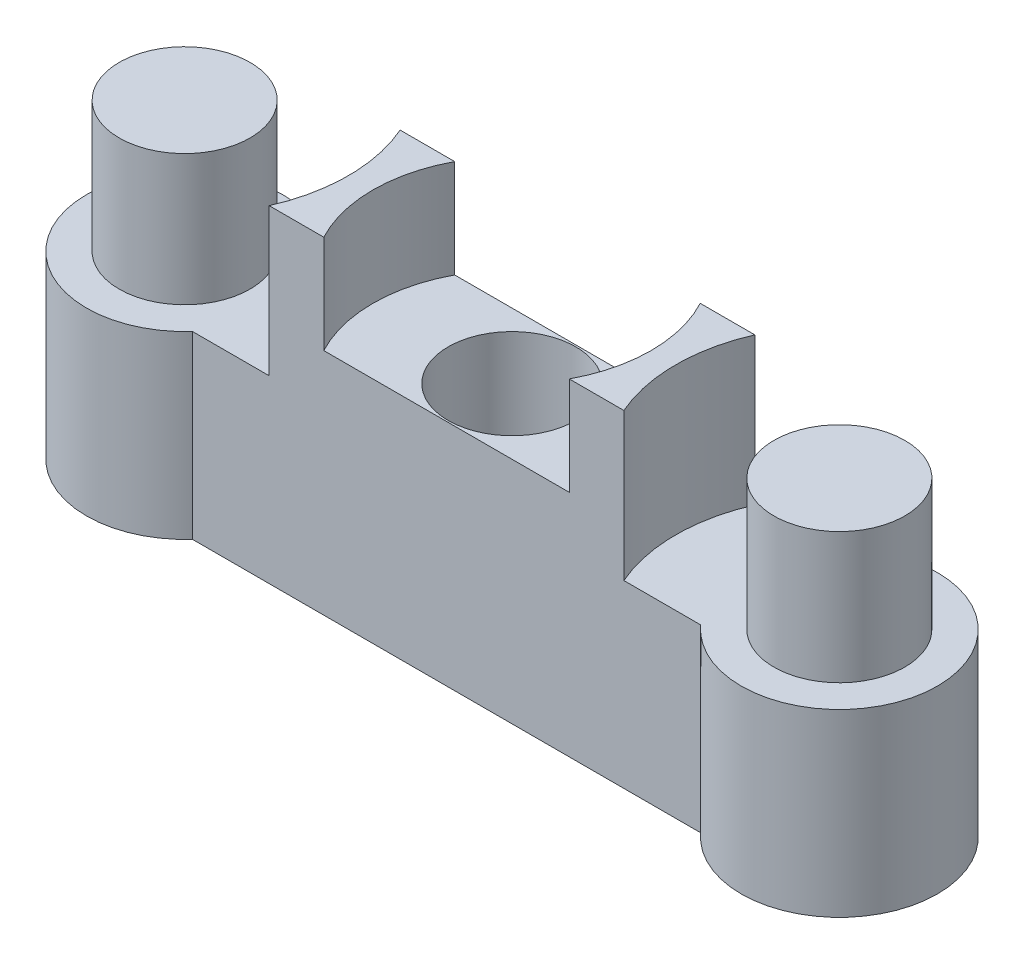
SolidWorks part; units mm, degrees
ref_plane "Front" through (0, 0, 0) normal (0, 0, 1) x (1, 0, 0)
ref_plane "Top" through (0, 0, 0) normal (0, 1, 0) x (1, 0, 0)
ref_plane "Right" through (0, 0, 0) normal (1, 0, 0) x (0, 0, -1)
sketch "草图1" plane through (0, 0, 0) normal (0, 1, 0) x (1, 0, 0)
  line L0 (0, 25.0119) -> (0, -20.6067) construction
  line L1 (-31.2771, 0) -> (37.836, 0) construction
  line L3 (7.7639, -2) -> (-7.7639, -2)
  line L5 (7.7639, 2) -> (-7.7639, 2)
  line L7 (7.7639, -2) -> (-7.7639, 2) construction
  line L8 (7.7639, 2) -> (-7.7639, -2) construction
  arc A0 (-7.7639, 2) -> (-7.7639, -2) centre (-10, 0) ccw
  arc A1 (7.7639, 2) -> (7.7639, -2) centre (10, 0) cw
  point P9 (0, 0)
  dimension "D2" = 6
  dimension "D1" = 4
  dimension "D3" = 10
extrude "凸台-拉伸1" add sketch "草图1" along normal blind 10
sketch "草图2" plane through (0, 10, 0) normal (0, 1, 0) x (1, 0, 0)
  line L0 (0, 19.2239) -> (0, -15.3802) construction
  circle A0 centre (-10, 0) radius 5
  circle A1 centre (10, 0) radius 5
  dimension "D1" = 10
extrude "切除-拉伸1" cut sketch "草图2" against normal blind 4.5
sketch "草图3" plane through (0, 5.5, 0) normal (0, 1, 0) x (1, 0, 0)
  line L0 (0, 14.6941) -> (0, -11.7424) construction
  circle A0 centre (-10, 0) radius 2
  circle A1 centre (10, 0) radius 2
  dimension "D1" = 4
extrude "凸台-拉伸2" add sketch "草图3" along normal blind 4
sketch "草图4" plane through (0, 10, 0) normal (0, 1, 0) x (1, 0, 0)
  circle A0 centre (0, 0) radius 1
  dimension "D1" = 2
extrude "切除-拉伸2" cut sketch "草图4" against normal through all
sketch "草图5" plane through (0, 10, 0) normal (0, 1, 0) x (1, 0, 0)
  circle A0 centre (0, 0) radius 1.95
  dimension "D1" = 3.9
extrude "切除-拉伸3" cut sketch "草图5" against normal blind 8
ref_plane "基准面1" through (0, 0, 0) normal (0, 1, 0) x (1, 0, 0)
sketch "草图6" plane through (0, 10, 0) normal (0, 1, 0) x (1, 0, 0)
  circle A0 centre (0, 0) radius 4.25
  dimension "D1" = 8.5
extrude "切除-拉伸4" cut sketch "草图6" against normal blind 3
